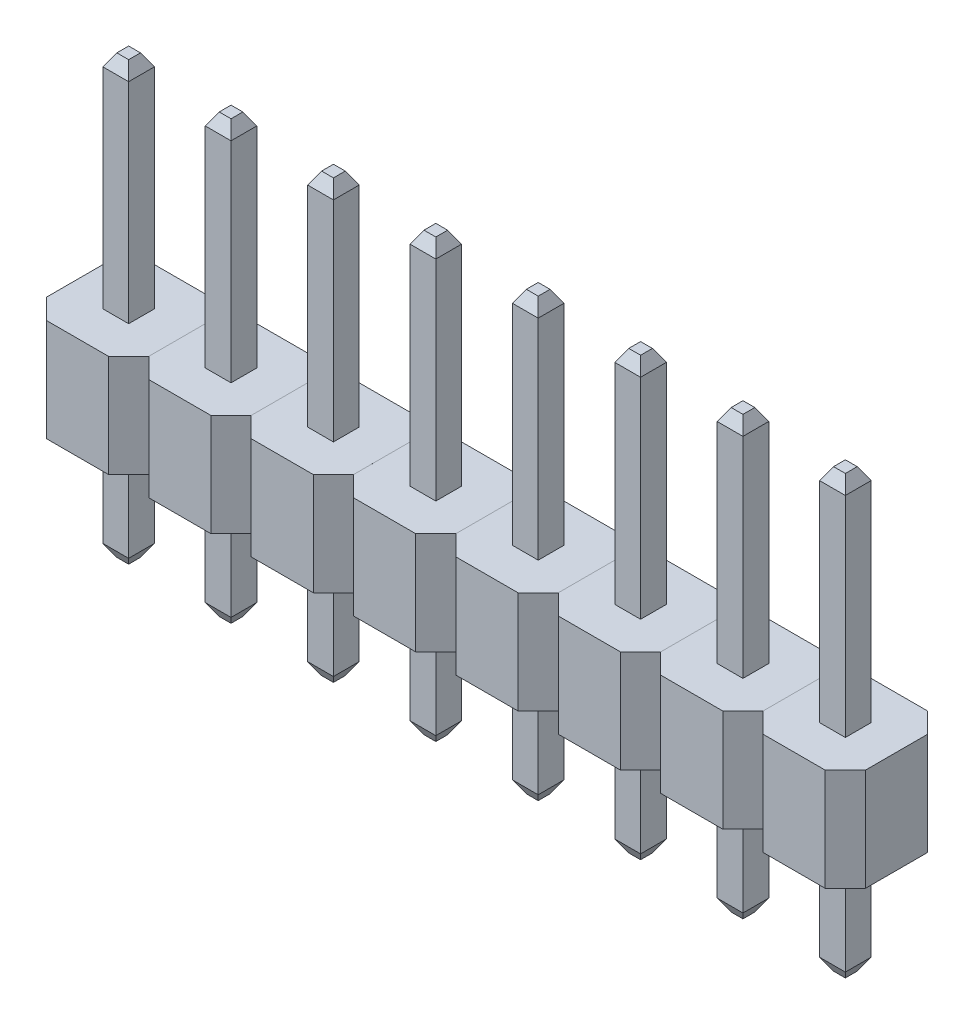
SolidWorks part; units mm, degrees
material "Male Header"
ref_plane "Front Plane" through (0, 0, 0) normal (0, 0, 1) x (1, 0, 0)
ref_plane "Top Plane" through (0, 0, 0) normal (0, 1, 0) x (1, 0, 0)
ref_plane "Right Plane" through (0, 0, 0) normal (1, 0, 0) x (0, 0, -1)
sketch "Sketch1" plane through (0, 0, 0) normal (0, 1, 0) x (1, 0, 0)
  line L1 (-1.27, -1.27) -> (1.27, -1.27)
  line L2 (-1.27, -1.27) -> (-1.27, 1.27)
  line L3 (-1.27, 1.27) -> (1.27, 1.27)
  line L4 (1.27, -1.27) -> (1.27, 1.27)
  line L5 (-1.27, -1.27) -> (1.27, 1.27) construction
  line L6 (-1.27, 1.27) -> (1.27, -1.27) construction
  point P0 (0, 0)
  dimension "D1" = 2.54
extrude "Boss-Extrude1" add sketch "Sketch1" along normal blind 2.54
chamfer "Chamfer1" distance 0.5 angle 45 4 edges at (-1.27, 1.27, -1.27) (-1.27, 1.27, 1.27) (1.27, 1.27, -1.27) (1.27, 1.27, 1.27)
sketch "Sketch2" plane through (0, 0, 0) normal (1, 0, 0) x (0, 0, -1)
  line L0 (0, 8.04) -> (0, -2.8)
  line L3 (-0.77, 2.54) -> (0.77, 2.54) construction
  dimension "D1" = 2.8
  dimension "D3" = 5.5
sketch "Sketch3" plane through (0, 0, 0) normal (0, 1, 0) x (1, 0, 0)
  line L1 (-0.32, -0.32) -> (0.32, -0.32)
  line L2 (-0.32, -0.32) -> (-0.32, 0.32)
  line L3 (-0.32, 0.32) -> (0.32, 0.32)
  line L4 (0.32, -0.32) -> (0.32, 0.32)
  line L5 (-0.32, -0.32) -> (0.32, 0.32) construction
  line L6 (-0.32, 0.32) -> (0.32, -0.32) construction
  point P0 (0, 0)
  dimension "D1" = 0.64
sweep "Sweep1" add profiles "Sketch3" path "Sketch2"
chamfer "Chamfer2" distance 0.3 angle 30 8 edges at (0, -2.8, 0.32) (-0.32, -2.8, 0) (0, -2.8, -0.32) (0.32, -2.8, 0) (0, 8.04, 0.32) (-0.32, 8.04, 0) (0, 8.04, -0.32) (0.32, 8.04, 0)
pattern_linear "LPattern1" [suppressed] count 2 spacing 2.54
pattern_linear "LPattern2" [suppressed] count 3 spacing 2.54
pattern_linear "LPattern3" [suppressed] count 4 spacing 2.54
pattern_linear "LPattern4" [suppressed] count 5 spacing 2.54
pattern_linear "LPattern5" [suppressed] count 6 spacing 2.54
pattern_linear "LPattern6" count 8 spacing 2.54 along (1, 0, 0) of bodies 102 101
pattern_linear "LPattern7" [suppressed] count 7 spacing 2.54
pattern_linear "LPattern8" [suppressed] count 2 spacing 2.54
